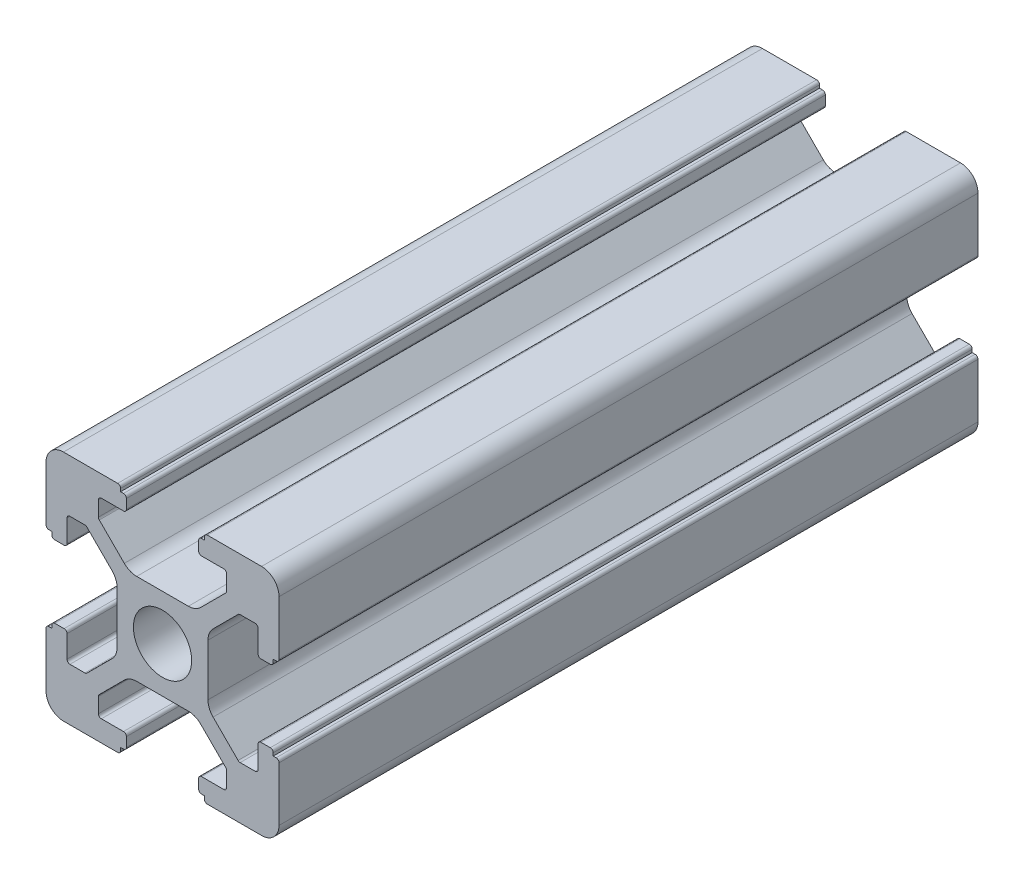
SolidWorks part; units mm, degrees
ref_plane "前视基准面" through (0, 0, 0) normal (0, 0, 1) x (1, 0, 0)
ref_plane "上视基准面" through (0, 0, 0) normal (0, 1, 0) x (1, 0, 0)
ref_plane "右视基准面" through (0, 0, 0) normal (1, 0, 0) x (0, 0, -1)
sketch "草图1" plane through (0, 0, 0) normal (0, 0, 1) x (1, 0, 0)
  line L0 (0, 0) -> (0, 5.5) construction
  line L1 (-8.5023, -10.0023) -> (-3.85, -10.0023)
  line L2 (-10.0023, -8.5023) -> (-10.0023, -3.85)
  line L3 (-8.5023, 10.0023) -> (-3.85, 10.0023)
  line L4 (10.0023, -8.5023) -> (10.0023, -3.85)
  line L5 (-10.0023, -10.0023) -> (10.0023, 10.0023) construction
  line L6 (-10.0023, 10.0023) -> (10.0023, -10.0023) construction
  line L7 (-2.218, -3.9) -> (2.218, -3.9)
  line L8 (-3.9, -2.218) -> (-3.9, 2.218)
  line L9 (-2.218, 3.9) -> (2.218, 3.9)
  line L10 (3.9, -2.218) -> (3.9, 2.218)
  line L11 (-3.9, -3.9) -> (3.9, 3.9) construction
  line L12 (-3.9, 3.9) -> (3.9, -3.9) construction
  line L13 (-5.25, -8.2) -> (-3.35, -8.2)
  line L14 (-8.2, -5.25) -> (-8.2, -3.35)
  line L15 (-5.25, 8.2) -> (-3.35, 8.2)
  line L16 (8.2, -5.25) -> (8.2, -3.35)
  line L17 (-8.2, -8.2) -> (8.2, 8.2) construction
  line L18 (-8.2, 8.2) -> (8.2, -8.2) construction
  line L19 (-7.95, 5.5) -> (-6.6642, 5.5)
  line L20 (0, 0) -> (5.5, 0) construction
  line L23 (-5.5, 7.95) -> (-5.5, 6.6642)
  line L26 (0, 0) -> (-0.5303, 0.5303)
  line L27 (3.2787, 4.3393) -> (5.4268, 6.4874)
  line L28 (0, 0) -> (0.5303, -0.5303)
  line L29 (5.5, 6.6642) -> (5.5, 7.95)
  line L30 (4.3393, 3.2787) -> (6.4874, 5.4268)
  line L31 (6.6642, 5.5) -> (7.95, 5.5)
  line L32 (4.3393, -3.2787) -> (6.4874, -5.4268)
  line L33 (3.2787, -4.3393) -> (5.4268, -6.4874)
  line L34 (-3.2787, -4.3393) -> (-5.4268, -6.4874)
  line L35 (-4.3393, -3.2787) -> (-6.4874, -5.4268)
  line L36 (-4.3393, 3.2787) -> (-6.4874, 5.4268)
  line L37 (-3.2787, 4.3393) -> (-5.4268, 6.4874)
  line L38 (3.1, -8.45) -> (3.1, -9.2523)
  line L39 (8.45, 3.1) -> (9.2523, 3.1)
  line L40 (-5.5, -6.6642) -> (-5.5, -7.95)
  line L41 (-6.6642, -5.5) -> (-7.95, -5.5)
  line L42 (5.5, -6.6642) -> (5.5, -7.95)
  line L43 (6.6642, -5.5) -> (7.95, -5.5)
  line L44 (9.2523, -3.1) -> (8.45, -3.1)
  line L46 (10.0023, 3.85) -> (10.0023, 8.5023)
  line L47 (8.2, 3.35) -> (8.2, 5.25)
  line L48 (-3.1, -9.2523) -> (-3.1, -8.45)
  line L49 (-8.45, -3.1) -> (-9.2523, -3.1)
  line L50 (-9.2523, 3.1) -> (-8.45, 3.1)
  line L51 (-3.1, 8.45) -> (-3.1, 9.2523)
  line L52 (3.1, 9.2523) -> (3.1, 8.45)
  line L53 (3.85, 10.0023) -> (8.5023, 10.0023)
  line L54 (3.35, 8.2) -> (5.25, 8.2)
  line L55 (-10.0023, 3.85) -> (-10.0023, 8.5023)
  line L56 (-8.2, 3.35) -> (-8.2, 5.25)
  line L57 (3.35, -8.2) -> (5.25, -8.2)
  line L58 (3.85, -10.0023) -> (8.5023, -10.0023)
  line L59 (9.7523, -3.6) -> (9.5023, -3.6)
  line L61 (9.7523, 3.6) -> (9.5023, 3.6)
  line L62 (9.5023, -3.6) -> (9.5023, -3.35)
  line L63 (3.6, -9.7523) -> (3.6, -9.5023)
  line L64 (3.35, -9.5023) -> (3.6, -9.5023)
  line L65 (9.5023, 3.35) -> (9.5023, 3.6)
  line L66 (-3.6, -9.5023) -> (-3.35, -9.5023)
  line L67 (-3.6, -9.7523) -> (-3.6, -9.5023)
  line L68 (-9.7523, -3.6) -> (-9.5023, -3.6)
  line L69 (-9.5023, -3.35) -> (-9.5023, -3.6)
  line L70 (-9.5023, 3.6) -> (-9.5023, 3.35)
  line L71 (-9.7523, 3.6) -> (-9.5023, 3.6)
  line L72 (-3.6, 9.7523) -> (-3.6, 9.5023)
  line L73 (-3.35, 9.5023) -> (-3.6, 9.5023)
  line L74 (3.6, 9.5023) -> (3.35, 9.5023)
  line L75 (3.6, 9.7523) -> (3.6, 9.5023)
  circle A0 centre (0, 0) radius 2.5
  arc A1 (10.0023, 8.5023) -> (8.5023, 10.0023) centre (8.5023, 8.5023) ccw
  arc A2 (8.5023, -10.0023) -> (10.0023, -8.5023) centre (8.5023, -8.5023) ccw
  arc A3 (-10.0023, -8.5023) -> (-8.5023, -10.0023) centre (-8.5023, -8.5023) ccw
  arc A4 (-10.0023, 8.5023) -> (-8.5023, 10.0023) centre (-8.5023, 8.5023) cw
  arc A5 (-9.5023, -3.35) -> (-9.2523, -3.1) centre (-9.2523, -3.35) cw
  arc A6 (-9.7523, -3.6) -> (-10.0023, -3.85) centre (-9.7523, -3.85) ccw
  arc A7 (-8.45, -3.1) -> (-8.2, -3.35) centre (-8.45, -3.35) cw
  arc A8 (-7.95, -5.5) -> (-8.2, -5.25) centre (-7.95, -5.25) cw
  arc A9 (-6.4874, -5.4268) -> (-6.6642, -5.5) centre (-6.6642, -5.25) cw
  arc A10 (-5.4268, -6.4874) -> (-5.5, -6.6642) centre (-5.25, -6.6642) ccw
  arc A11 (-5.5, -7.95) -> (-5.25, -8.2) centre (-5.25, -7.95) ccw
  arc A12 (-3.6, -9.7523) -> (-3.85, -10.0023) centre (-3.85, -9.7523) cw
  arc A13 (-3.35, -9.5023) -> (-3.1, -9.2523) centre (-3.35, -9.2523) ccw
  arc A14 (-3.1, -8.45) -> (-3.35, -8.2) centre (-3.35, -8.45) ccw
  arc A15 (3.1, -8.45) -> (3.35, -8.2) centre (3.35, -8.45) cw
  arc A16 (5.5, -7.95) -> (5.25, -8.2) centre (5.25, -7.95) cw
  arc A17 (5.4268, -6.4874) -> (5.5, -6.6642) centre (5.25, -6.6642) cw
  arc A18 (6.4874, -5.4268) -> (6.6642, -5.5) centre (6.6642, -5.25) ccw
  arc A19 (7.95, -5.5) -> (8.2, -5.25) centre (7.95, -5.25) ccw
  arc A20 (8.45, -3.1) -> (8.2, -3.35) centre (8.45, -3.35) ccw
  arc A21 (9.5023, -3.35) -> (9.2523, -3.1) centre (9.2523, -3.35) ccw
  arc A22 (9.7523, -3.6) -> (10.0023, -3.85) centre (9.7523, -3.85) cw
  arc A23 (3.35, -9.5023) -> (3.1, -9.2523) centre (3.35, -9.2523) cw
  arc A24 (3.6, -9.7523) -> (3.85, -10.0023) centre (3.85, -9.7523) ccw
  arc A25 (7.95, 5.5) -> (8.2, 5.25) centre (7.95, 5.25) cw
  arc A26 (8.2, 3.35) -> (8.45, 3.1) centre (8.45, 3.35) ccw
  arc A27 (9.5023, 3.35) -> (9.2523, 3.1) centre (9.2523, 3.35) cw
  arc A28 (9.7523, 3.6) -> (10.0023, 3.85) centre (9.7523, 3.85) ccw
  arc A29 (6.6642, 5.5) -> (6.4874, 5.4268) centre (6.6642, 5.25) ccw
  arc A30 (5.4268, 6.4874) -> (5.5, 6.6642) centre (5.25, 6.6642) ccw
  arc A31 (5.5, 7.95) -> (5.25, 8.2) centre (5.25, 7.95) ccw
  arc A32 (3.1, 8.45) -> (3.35, 8.2) centre (3.35, 8.45) ccw
  arc A33 (3.6, 9.7523) -> (3.85, 10.0023) centre (3.85, 9.7523) cw
  arc A34 (3.35, 9.5023) -> (3.1, 9.2523) centre (3.35, 9.2523) ccw
  arc A35 (-9.7523, 3.6) -> (-10.0023, 3.85) centre (-9.7523, 3.85) cw
  arc A36 (-9.5023, 3.35) -> (-9.2523, 3.1) centre (-9.2523, 3.35) ccw
  arc A37 (-8.45, 3.1) -> (-8.2, 3.35) centre (-8.45, 3.35) ccw
  arc A38 (-8.2, 5.25) -> (-7.95, 5.5) centre (-7.95, 5.25) cw
  arc A39 (-6.4874, 5.4268) -> (-6.6642, 5.5) centre (-6.6642, 5.25) ccw
  arc A40 (-5.4268, 6.4874) -> (-5.5, 6.6642) centre (-5.25, 6.6642) cw
  arc A41 (-5.5, 7.95) -> (-5.25, 8.2) centre (-5.25, 7.95) cw
  arc A42 (-3.1, 8.45) -> (-3.35, 8.2) centre (-3.35, 8.45) cw
  arc A43 (-3.1, 9.2523) -> (-3.35, 9.5023) centre (-3.35, 9.2523) ccw
  arc A44 (-3.6, 9.7523) -> (-3.85, 10.0023) centre (-3.85, 9.7523) ccw
  arc A45 (-4.3393, 3.2787) -> (-3.9, 2.218) centre (-5.4, 2.218) cw
  arc A46 (-3.2787, 4.3393) -> (-2.218, 3.9) centre (-2.218, 5.4) ccw
  arc A47 (3.2787, 4.3393) -> (2.218, 3.9) centre (2.218, 5.4) cw
  arc A48 (4.3393, 3.2787) -> (3.9, 2.218) centre (5.4, 2.218) ccw
  arc A49 (4.3393, -3.2787) -> (3.9, -2.218) centre (5.4, -2.218) cw
  arc A50 (3.2787, -4.3393) -> (2.218, -3.9) centre (2.218, -5.4) ccw
  arc A51 (-4.3393, -3.2787) -> (-3.9, -2.218) centre (-5.4, -2.218) ccw
  arc A52 (-2.218, -3.9) -> (-3.2787, -4.3393) centre (-2.218, -5.4) ccw
  point P0 (0, 0)
  point P7 (10.0023, 0)
  point P62 (0, 0)
  point P76 (0, 0)
  point P92 (-8.2, -5.5)
  point P99 (0, 0)
  point P106 (-5.5, -8.2)
  point P117 (5.5, -8.2)
  point P124 (8.2, -5.5)
  point P137 (8.2, 5.5)
  point P140 (8.2, 3.1)
  point P147 (6.5607, 5.5)
  point P152 (5.5, 8.2)
  point P167 (-8.2, 5.5)
  point P174 (-5.5, 8.2)
  dimension "D1" = 1.5
  dimension "D5" = 0.25
  dimension "D6" = 1.5
  dimension "D2" = 4
  dimension "D3" = 4
  dimension "D4" = 4
extrude "凸台-拉伸1" add sketch "草图1" along normal blind 60 contours A52 L7 A50 L33 A17 L42 A16 L57 A15 L38 A23 L64 L63 A24 L58 A2 L4 A22 L59 L62 A21 L44 A20 L16 A19 L43 A18 L32 A49 L10 A48 L30 A29 L31 A25 L47 A26 L39 A27 L65 L61 A28 L46 A1 L53 A33 L75 L74 A34 L52 A32
